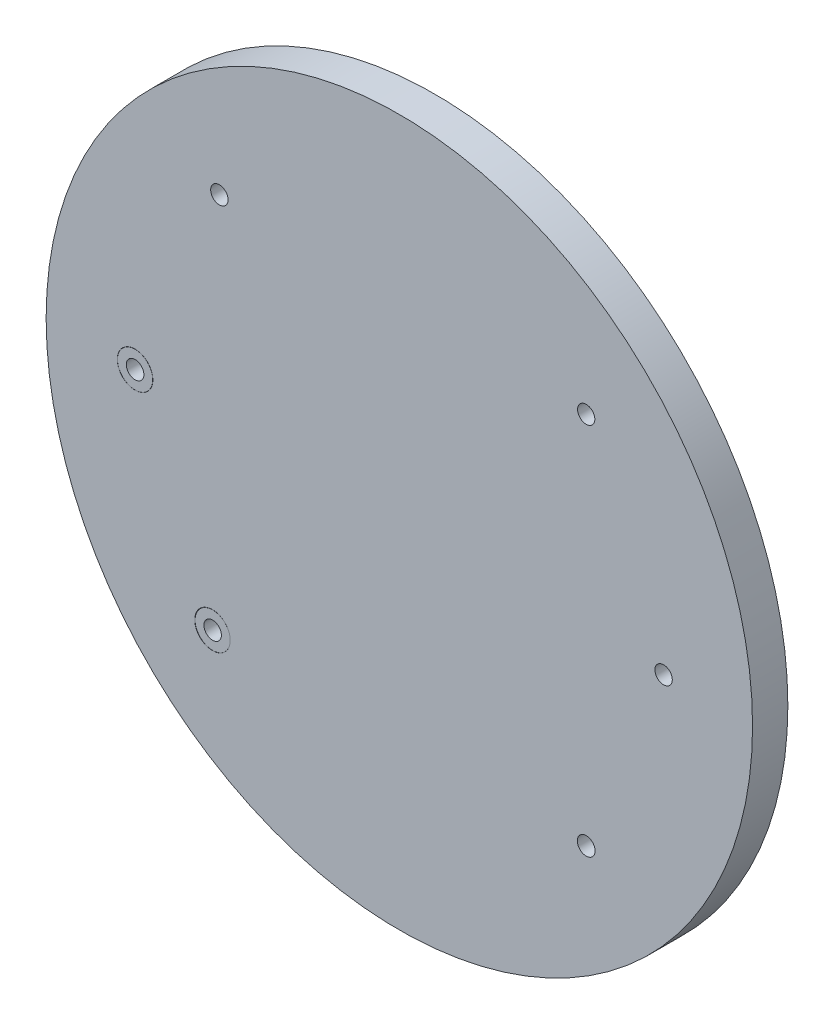
SolidWorks part; units mm, degrees
ref_plane "Front Plane" through (0, 0, 0) normal (0, 0, 1) x (1, 0, 0)
ref_plane "Top Plane" through (0, 0, 0) normal (0, 1, 0) x (1, 0, 0)
ref_plane "Right Plane" through (0, 0, 0) normal (1, 0, 0) x (0, 0, -1)
sketch "Sketch1" plane through (0, 0, 0) normal (0, 0, 1) x (1, 0, 0)
  circle A0 centre (0, 0) radius 100.0402
  circle A2 centre (52.9242, -52.9242) radius 4.9998
  circle A3 centre (74.8461, 0) radius 4.9941
  circle A4 centre (52.9242, 52.9242) radius 4.9855
  circle A5 centre (-52.9242, -52.9242) radius 5.0247
  circle A6 centre (-74.8461, 0) radius 5.0344
  circle A7 centre (-50.9662, 54.8122) radius 5.0057
extrude "Boss-Extrude1" add sketch "Sketch1" along normal blind 10
sketch "Sketch2" plane through (0, 0, 0) normal (0, 0, -1) x (-1, 0, 0)
  circle A1 centre (-74.8461, 0) radius 2.463
  circle A2 centre (-74.8461, 0) radius 4.9941
extrude "Boss-Extrude2" add sketch "Sketch2" against normal blind 10
sketch "Sketch3" plane through (0, 0, 0) normal (0, 0, -1) x (-1, 0, 0)
  circle A0 centre (74.8461, 0) radius 4.99
  circle A1 centre (-52.9242, -52.9242) radius 2.5199
  circle A2 centre (-52.9242, -52.9242) radius 4.9998
  circle A4 centre (52.8757, -52.9242) radius 2.4728
  circle A5 centre (52.8757, -52.9242) radius 4.9763
  circle A6 centre (74.8461, 0) radius 2.4953
  circle A7 centre (50.9662, 54.8122) radius 2.4725
  circle A8 centre (50.9662, 54.8122) radius 5.0057
  circle A10 centre (-52.9242, 52.9242) radius 2.4473
  circle A11 centre (-52.9242, 52.9242) radius 4.9855
extrude "Boss-Extrude4" add sketch "Sketch3" against normal blind 10
